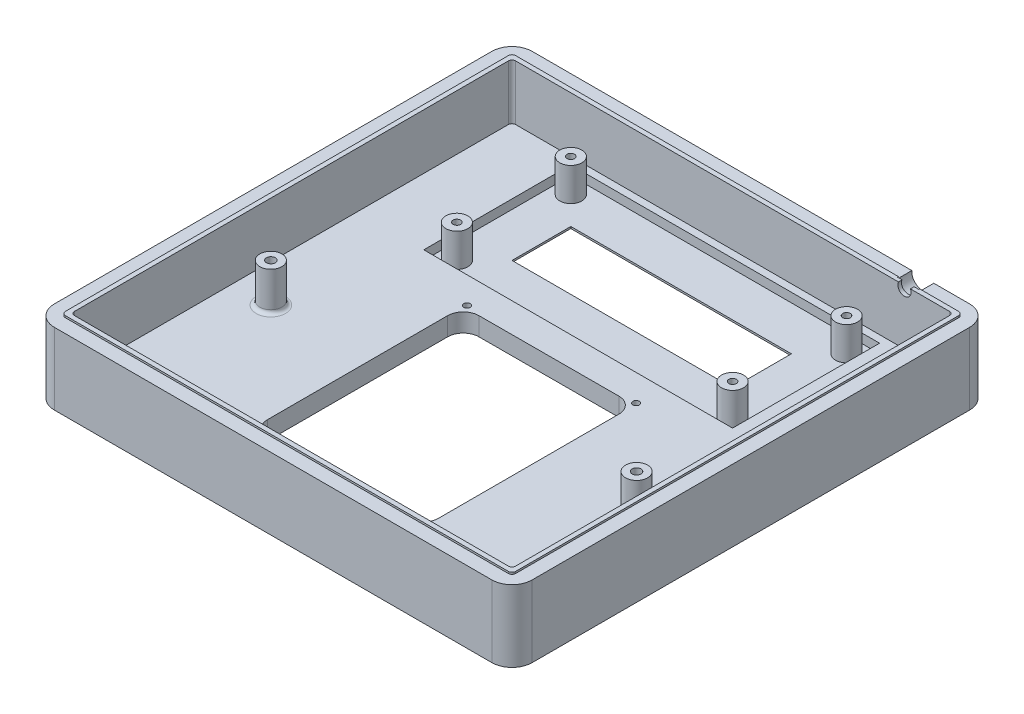
SolidWorks part; units mm, degrees
ref_plane "Front" through (0, 0, 0) normal (0, 0, 1) x (1, 0, 0)
ref_plane "Top" through (0, 0, 0) normal (0, 1, 0) x (1, 0, 0)
ref_plane "Right" through (0, 0, 0) normal (1, 0, 0) x (0, 0, -1)
sketch "Sketch4" plane through (0, 0, 0) normal (0, 1, 0) x (1, 0, 0)
  line L12 (-59.5, 65) -> (59.5, 65)
  line L13 (-65, 59.5) -> (-65, -59.5)
  line L14 (-59.5, -65) -> (59.5, -65)
  line L15 (65, -59.5) -> (65, 59.5)
  arc A0 (65, 59.5) -> (59.5, 65) centre (59.5, 59.5) ccw
  arc A1 (-65, 59.5) -> (-59.5, 65) centre (-59.5, 59.5) cw
  arc A2 (-59.5, -65) -> (-65, -59.5) centre (-59.5, -59.5) cw
  arc A3 (65, -59.5) -> (59.5, -65) centre (59.5, -59.5) cw
  dimension "D1" = 5.5
  dimension "D2" = 119
extrude "Boss-Extrude2" add sketch "Sketch4" along normal blind 20
sketch "Sketch5" plane through (0, 20, 0) normal (0, 1, 0) x (1, 0, 0)
  line L3 (-60, -60) -> (60, -60)
  line L4 (-60, -60) -> (-60, 60)
  line L5 (-60, 60) -> (60, 60)
  line L6 (60, -60) -> (60, 60)
extrude "Cut-Extrude1" cut sketch "Sketch5" against normal blind 15
fillet "Fillet2" radius 1 1 edges at (-60, 12.5, -60)
fillet "Fillet3" radius 1 1 edges at (60, 12.5, -60)
fillet "Fillet4" radius 1 1 edges at (-60, 12.5, 60)
fillet "Fillet5" radius 1 1 edges at (60, 12.5, 60)
sketch "Sketch6" plane through (0, 5, 0) normal (0, 1, 0) x (1, 0, 0)
  line L5 (-19, 10) -> (19, 10.0748)
  line L6 (-23.25, 5.75) -> (-23.25, -43.25)
  line L7 (-19, -47.5) -> (19, -47.5)
  line L8 (23.25, 5.8248) -> (23.25, -43.25)
  arc A0 (-19, -47.5) -> (-23.25, -43.25) centre (-19, -43.25) cw
  arc A1 (-19, 10) -> (-23.25, 5.75) centre (-19, 5.75) ccw
  arc A2 (23.25, 5.8248) -> (19, 10.0748) centre (19, 5.8248) ccw
  arc A3 (19, -47.5) -> (23.25, -43.25) centre (19, -43.25) ccw
  dimension "D3" = 4.25
  dimension "D1" = 49
  dimension "D2" = 38
extrude "Cut-Extrude2" cut sketch "Sketch6" against normal blind 5
sketch "Sketch8" plane through (0, 5, 0) normal (0, 1, 0) x (1, 0, 0)
  line L4 (-30, 30) -> (30, 30)
  line L5 (-30, 30) -> (-30, 46)
  line L6 (-30, 46) -> (30, 46)
  line L7 (30, 30) -> (30, 46)
extrude "Cut-Extrude5" cut sketch "Sketch8" against normal blind 5
sketch "Sketch9" plane through (0, 5, 0) normal (0, 1, 0) x (1, 0, 0)
  line L4 (-42, 18) -> (42, 18)
  line L5 (-42, 18) -> (-42, 58)
  line L6 (-42, 58) -> (42, 58)
  line L7 (42, 18) -> (42, 58)
extrude "Cut-Extrude6" cut sketch "Sketch9" against normal blind 2.5
sketch "Sketch10" plane through (0, 2.5, 0) normal (0, 1, 0) x (1, 0, 0)
  circle A0 centre (37.5, 53.5) radius 3
  circle A1 centre (-37.5, 53.5) radius 3
  circle A2 centre (-37.5, 22.5) radius 3
  circle A3 centre (37.5, 22.5) radius 3
extrude "Boss-Extrude3" add sketch "Sketch10" along normal blind 9 contours A2 | A0 | A1 | A3
chamfer "Chamfer1" distance 2 angle 45 4 edges at (0, 0, -30) (-30, 0, -38) (0, 0, -46) (30, 0, -38)
sketch "Sketch11" plane through (0, 11.5, 0) normal (0, 1, 0) x (1, 0, 0)
  circle A0 centre (-37.5, 53.5) radius 1.025
sketch "Sketch12" plane through (0, 11.5, 0) normal (0, 1, 0) x (1, 0, 0)
  circle A0 centre (-37.5, 22.5) radius 1.025
sketch "Sketch13" plane through (0, 11.5, 0) normal (0, 1, 0) x (1, 0, 0)
  circle A0 centre (37.5, 53.5) radius 1.025
sketch "Sketch14" plane through (0, 11.5, 0) normal (0, 1, 0) x (1, 0, 0)
  circle A0 centre (37.5, 22.5) radius 1.025
sketch "Sketch15" plane through (0, 0, -65) normal (0, 0, -1) x (-1, 0, 0)
  line L0 (-45.1183, 20) -> (-48.3817, 20)
  arc A1 (-45.1183, 20) -> (-48.3817, 20) centre (-46.75, 19.24) cw
extrude "Cut-Extrude11" cut sketch "Sketch15" against normal blind 5
sketch "Sketch16" plane through (0, 0, -65) normal (0, 0, -1) x (-1, 0, 0)
  line L0 (-43.8479, 20) -> (-49.6521, 20)
  arc A2 (-49.6521, 20) -> (-43.8479, 20) centre (-46.75, 19.24) ccw
extrude "Cut-Extrude12" cut sketch "Sketch16" against normal blind 4
sketch "Sketch17" plane through (0, 5, 0) normal (0, 1, 0) x (1, 0, 0)
  circle A0 centre (49.7, -15.8) radius 3
  circle A1 centre (-49.8, -15.8) radius 3
  point P5 (49.7, -15.8)
extrude "Boss-Extrude4" add sketch "Sketch17" along normal blind 10.54
sketch "Sketch18" plane through (0, 15.54, 0) normal (0, 1, 0) x (1, 0, 0)
  circle A0 centre (-49.8, -15.8) radius 1.2
sketch "Sketch19" plane through (0, 15.54, 0) normal (0, 1, 0) x (1, 0, 0)
  circle A0 centre (49.7, -15.8) radius 1.2
sketch "Sketch20" plane through (0, 20, 0) normal (0, 1, 0) x (1, 0, 0)
  line L0 (-59.5, -65) -> (59.5, -65)
  line L1 (65, -59.5) -> (65, 59.5)
  line L2 (59.5, 65) -> (-59.5, 65)
  line L3 (-61.25, -61.25) -> (61.25, -61.25)
  line L4 (-61.25, -61.25) -> (-61.25, 61.25)
  line L5 (-61.25, 61.25) -> (61.25, 61.25)
  line L6 (61.25, -61.25) -> (61.25, 61.25)
  line L7 (-65, 59.5) -> (-65, -59.5)
  arc A0 (59.5, -65) -> (65, -59.5) centre (59.5, -59.5) ccw construction
  arc A1 (59.5, -65) -> (65, -59.5) centre (59.5, -59.5) ccw
  arc A2 (-65, -59.5) -> (-59.5, -65) centre (-59.5, -59.5) ccw
  arc A3 (-59.5, 65) -> (-65, 59.5) centre (-59.5, 59.5) ccw
  arc A4 (59.5, 65) -> (65, 59.5) centre (59.5, 59.5) cw
extrude "Cut-Extrude15" cut sketch "Sketch20" against normal blind 0.5
fillet "Fillet7" radius 1 1 edges at (61.25, 19.75, 61.25)
fillet "Fillet8" radius 1 1 edges at (-61.25, 19.75, 61.25)
fillet "Fillet9" radius 1 1 edges at (-61.25, 19.75, -61.25)
fillet "Fillet10" radius 1 1 edges at (61.25, 19.75, -61.25)
extrude "Cut-Extrude20" cut sketch "Sketch19" against normal blind 6 contours A0
extrude "Cut-Extrude21" cut sketch "Sketch18" against normal blind 6 contours A0
extrude "Cut-Extrude22" cut sketch "Sketch11" against normal blind 6 contours A0
extrude "Cut-Extrude23" cut sketch "Sketch13" against normal blind 6 contours A0
extrude "Cut-Extrude24" cut sketch "Sketch12" against normal blind 6 contours A0
extrude "Cut-Extrude25" cut sketch "Sketch14" against normal blind 6 contours A0
sketch "Sketch24" plane through (0, 5, 0) normal (0, 1, 0) x (1, 0, 0)
  circle A1 centre (23, 10.7687) radius 0.875
  circle A2 centre (-23, 10.7687) radius 0.875
  circle A3 centre (-23, -48.2313) radius 0.875
  circle A4 centre (23, -48.2313) radius 0.875
extrude "Cut-Extrude28" cut sketch "Sketch24" against normal blind 3
fillet "Fillet11" radius 1 1 edges at (-49.8, 5, 12.8)
fillet "Fillet12" radius 1 1 edges at (49.7, 5, 12.8)
